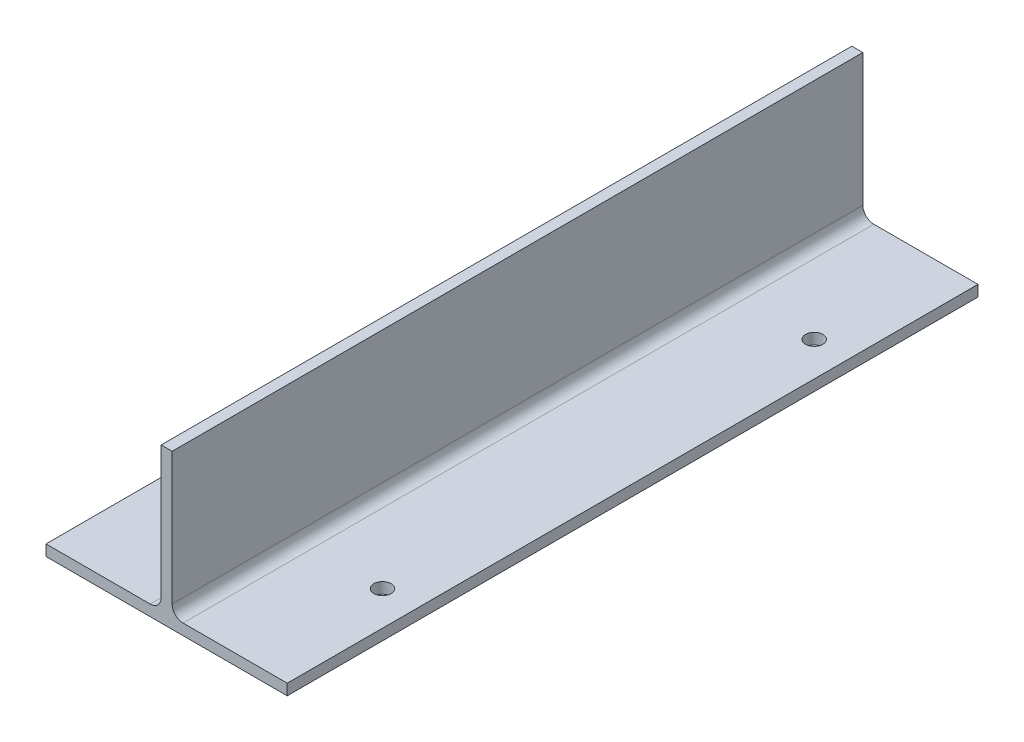
SolidWorks part; units mm, degrees
material "AISI 1020"
ref_plane "Plano frontal" through (0, 0, 0) normal (0, 0, 1) x (1, 0, 0)
ref_plane "Plano superior" through (0, 0, 0) normal (0, 1, 0) x (1, 0, 0)
ref_plane "Plano direito" through (0, 0, 0) normal (1, 0, 0) x (0, 0, -1)
sketch "Esboço1" plane through (0, 0, 0) normal (0, 0, 1) x (1, 0, 0)
  line L0 (0, 0) -> (0, 153.6292) construction
  line L1 (-69.85, 0) -> (69.85, 0)
  line L2 (69.85, 0) -> (69.85, 6.35)
  line L3 (69.85, 6.35) -> (9.525, 6.35)
  line L4 (3.175, 12.7) -> (3.175, 89.3)
  line L5 (3.175, 89.3) -> (-3.175, 89.3)
  line L6 (-3.175, 12.7) -> (-3.175, 89.3)
  line L7 (-69.85, 6.35) -> (-9.525, 6.35)
  line L8 (-69.85, 0) -> (-69.85, 6.35)
  arc A0 (9.525, 6.35) -> (3.175, 12.7) centre (9.525, 12.7) cw
  arc A1 (-9.525, 6.35) -> (-3.175, 12.7) centre (-9.525, 12.7) ccw
  point P14 (0, 89.3)
  dimension "D5" = 6.35
  dimension "D1" = 89.3
  dimension "D2" = 6.35
  dimension "D3" = 139.7
  dimension "D4" = 6.35
extrude "Ressalto-extrusão1" add sketch "Esboço1" along normal blind 400
sketch "Esboço2" plane through (0, 6.35, 0) normal (0, 1, 0) x (1, 0, 0)
  line L0 (0, 0) -> (0, -400) construction
  line L1 (3.175, -400) -> (-3.175, -400) construction
  circle A0 centre (50, -75) radius 5
  circle A1 centre (-50, -75) radius 5
  circle A2 centre (50, -325) radius 5
  circle A3 centre (-50, -325) radius 5
  dimension "D1" = 10
  dimension "D2" = 100
  dimension "D3" = 75
  dimension "D4" = 2
extrude "Corte-extrusão1" cut sketch "Esboço2" against normal through all
equation "\"D4@Esboço1\"=\"D2@Esboço1\""
